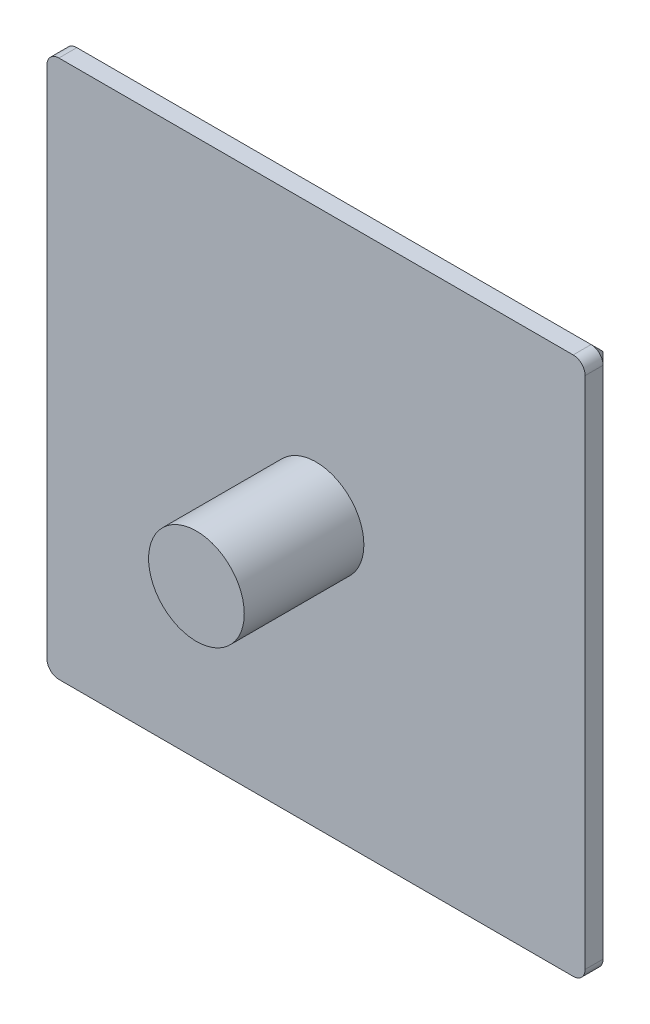
SolidWorks part; units mm, degrees
ref_plane "Plan de face" through (0, 0, 0) normal (0, 0, 1) x (1, 0, 0)
ref_plane "Plan de dessus" through (0, 0, 0) normal (0, 1, 0) x (1, 0, 0)
ref_plane "Plan de droite" through (0, 0, 0) normal (1, 0, 0) x (0, 0, -1)
sketch "Sketch1" plane through (0, 0, 0) normal (0, 0, 1) x (1, 0, 0)
  line L1 (22.5, -22.5) -> (-22.5, -22.5)
  line L2 (22.5, -22.5) -> (22.5, 22.5)
  line L3 (22.5, 22.5) -> (-22.5, 22.5)
  line L4 (-22.5, -22.5) -> (-22.5, 22.5)
  line L5 (22.5, -22.5) -> (-22.5, 22.5) construction
  line L6 (22.5, 22.5) -> (-22.5, -22.5) construction
  point P0 (0, 0)
  dimension "D1" = 45
  dimension "D2" = 45
extrude "Boss-Extrude1" add sketch "Sketch1" along normal blind 2.5
fillet "Fillet1" radius 1 4 edges at (-22.5, -22.5, 1.25) (22.5, -22.5, 1.25) (-22.5, 22.5, 1.25) (22.5, 22.5, 1.25)
sketch "Sketch2" plane through (0, 0, 2.5) normal (0, 0, 1) x (1, 0, 0)
  circle A0 centre (0, 0) radius 4
  dimension "D1" = 8
extrude "Boss-Extrude2" add sketch "Sketch2" along normal blind 10
chamfer "Chamfer1" distance 1 angle 45 8 edges at (0, -22.5, 0) (22.5, 0, 0) (0, 22.5, 0) (-22.5, 0, 0) (22.2071, -22.2071, 0) (22.2071, 22.2071, 0) (-22.2071, 22.2071, 0) (-22.2071, -22.2071, 0)
